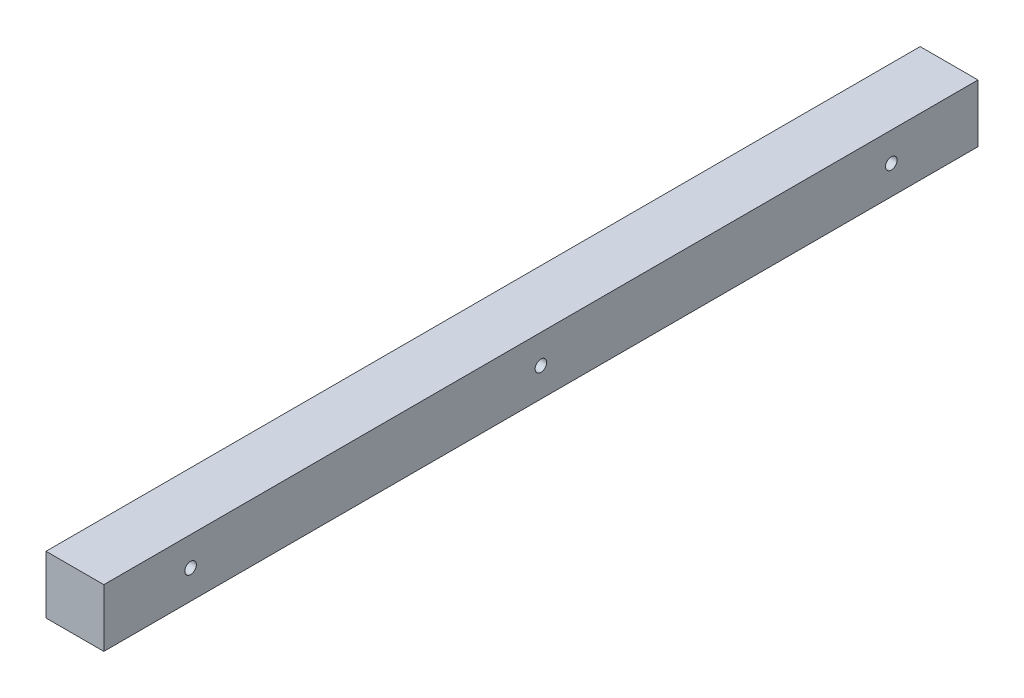
SolidWorks part; units mm, degrees
ref_plane "Front Plane" through (0, 0, 0) normal (0, 0, 1) x (1, 0, 0)
ref_plane "Top Plane" through (0, 0, 0) normal (0, 1, 0) x (1, 0, 0)
ref_plane "Right Plane" through (0, 0, 0) normal (1, 0, 0) x (0, 0, -1)
sketch "Sketch1" plane through (0, 0, 0) normal (0, 0, 1) x (1, 0, 0)
  line L1 (0, 0) -> (20, 0)
  line L2 (0, 0) -> (0, 20)
  line L3 (0, 20) -> (20, 20)
  line L4 (20, 0) -> (20, 20)
  dimension "D1" = 20
  dimension "D2" = 20
extrude "Boss-Extrude1" add sketch "Sketch1" along normal blind 302.33
sketch "Sketch2" plane through (0, 0, 0) normal (-1, 0, 0) x (0, 0, 1)
  line L0 (17.0382, 0) -> (-32.1317, 70.2218) construction
  line L1 (17.0382, 0) -> (-32.1317, 70.2218) construction
  line L2 (332.908, 70.2218) -> (283.7382, 0) construction
  line L3 (332.908, 70.2218) -> (283.7382, 0) construction
  line L4 (302.33, 0) -> (0, 0) construction
  line L5 (302.33, 0) -> (0, 0) construction
  line L6 (0, 10) -> (307.3744, 10) construction
  line L7 (0, 20) -> (0, 0) construction
  line L8 (151.165, 0) -> (151.165, 33.0002) construction
  line L9 (0, 0) -> (0, 20) construction
  line L10 (302.33, 0) -> (302.33, 20) construction
  circle A0 centre (30, 10) radius 2
  circle A1 centre (272.33, 10) radius 2
  circle A2 centre (151.165, 10) radius 2
  dimension "D1" = 4
  dimension "D3" = 4
  dimension "D5" = 4
  dimension "D2" = 30
  dimension "D4" = 30
extrude "Cut-Extrude1" cut sketch "Sketch2" against normal through all
